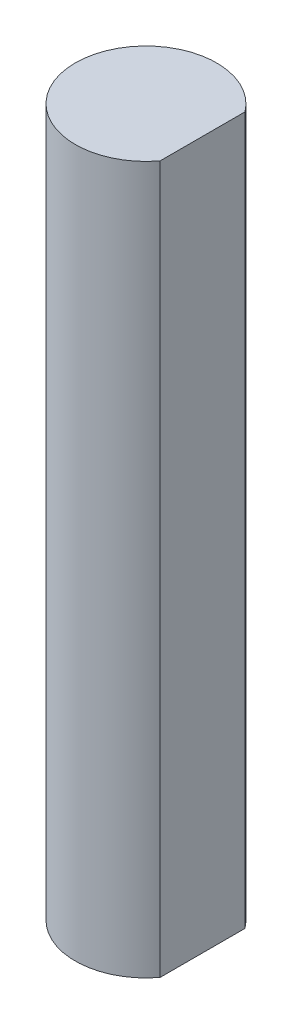
SolidWorks part; units mm, degrees
ref_plane "Front Plane" through (0, 0, 0) normal (0, 0, 1) x (1, 0, 0)
ref_plane "Top Plane" through (0, 0, 0) normal (0, 1, 0) x (1, 0, 0)
ref_plane "Right Plane" through (0, 0, 0) normal (1, 0, 0) x (0, 0, -1)
sketch "Sketch1" plane through (0, 0, 0) normal (0, 1, 0) x (1, 0, 0)
  line L0 (0, 0) -> (2.54, 0) construction
  line L1 (2.54, 3.81) -> (2.54, -3.81)
  circle A0 centre (0, 0) radius 3.175
  point P6 (2.54, 0)
  dimension "D1" = 6.35
  dimension "D2" = 2.54
  dimension "D3" = 7.62
extrude "Boss-Extrude1" add sketch "Sketch1" along normal blind 31.75
equation "\"D2@Sketch1\"=.125-.025"
